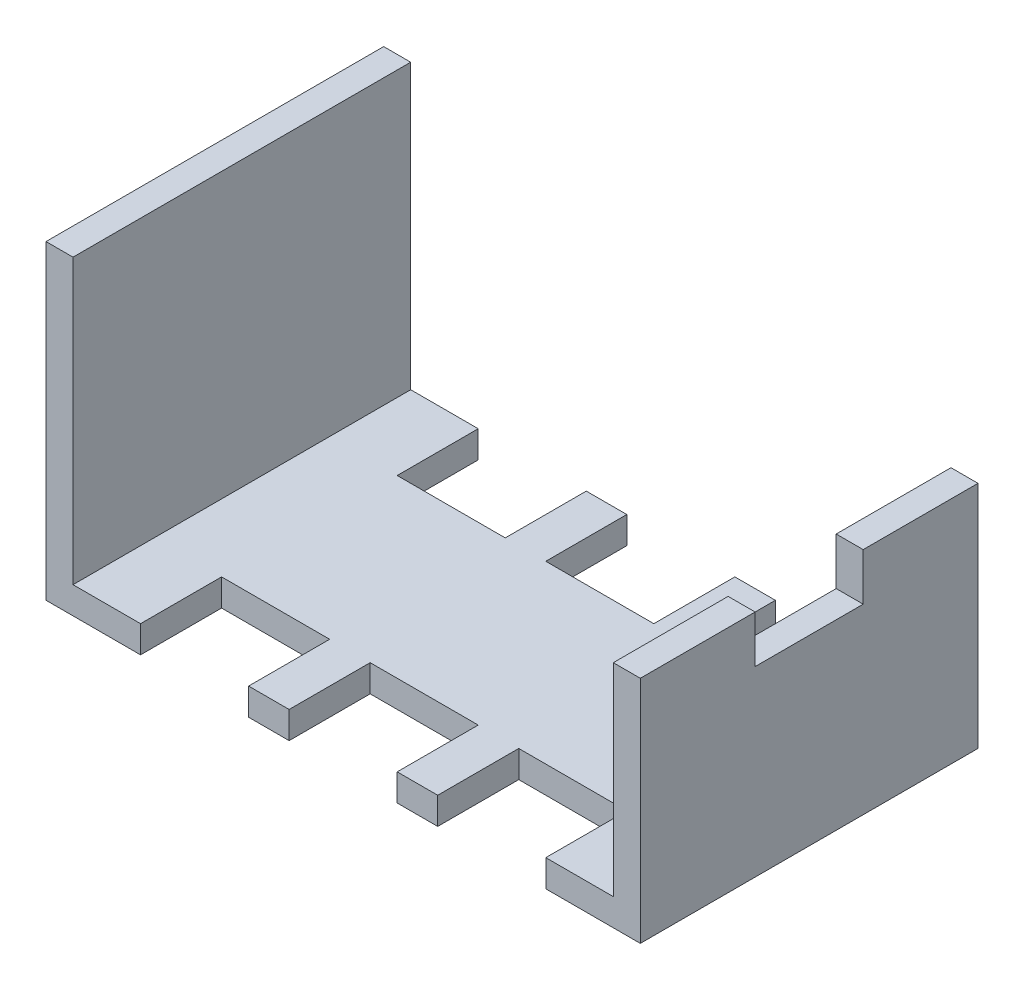
SolidWorks part; units mm, degrees
ref_plane "Front Plane" through (0, 0, 0) normal (0, 0, 1) x (1, 0, 0)
ref_plane "Top Plane" through (0, 0, 0) normal (0, 1, 0) x (1, 0, 0)
ref_plane "Right Plane" through (0, 0, 0) normal (1, 0, 0) x (0, 0, -1)
sketch "Sketch2" plane through (0, 0, 0) normal (0, 1, 0) x (1, 0, 0)
  line L1 (-22, 14.5) -> (22, 14.5)
  line L2 (-22, 14.5) -> (-22, -14.5)
  line L3 (-22, -14.5) -> (22, -14.5)
  line L4 (22, 14.5) -> (22, -14.5)
  line L5 (-22, 14.5) -> (22, -14.5) construction
  line L6 (-22, -14.5) -> (22, 14.5) construction
  point P0 (0, 0)
extrude "Boss-Extrude1" add sketch "Sketch2" along normal blind 23
sketch "Sketch3" plane through (0, 23, 0) normal (0, 1, 0) x (1, 0, 0)
  line L5 (-20, 12.5) -> (20, 12.5)
  line L6 (-20, 12.5) -> (-20, -12.5)
  line L7 (-20, -12.5) -> (20, -12.5)
  line L8 (20, 12.5) -> (20, -12.5)
  line L9 (-20, 12.5) -> (20, -12.5) construction
  line L10 (-20, -12.5) -> (20, 12.5) construction
  point P0 (0, 0)
  point P1 (0, 0)
extrude "Cut-Extrude1" cut sketch "Sketch3" against normal blind 21 contours L6 L5 L8 L7
sketch "Sketch4" plane through (0, 0, 14.5) normal (0, 0, 1) x (1, 0, 0)
  line L0 (-22, 23) -> (-20.1, 23) construction
  line L1 (-22, 23) -> (22, 23) construction
  line L2 (-20.1, 23) -> (-10.1, 23) construction
  line L3 (-10.1, 23) -> (-10.1, 17.2) construction
  line L4 (-10.1, 17.2) -> (10.6, 17.2) construction
  line L5 (-10.1, 17.2) -> (10.6, 17.2)
  line L6 (-10.1, 17.2) -> (-10.1, 19.2)
  line L7 (10.6, 17.2) -> (10.6, 19.2)
  line L8 (-10.1, 19.2) -> (10.6, 19.2)
  line L10 (-20.1, 23) -> (-20.1, 2) construction
  line L11 (-20.1, 2) -> (-15.1, 2) construction
  line L12 (20.2, 2) -> (20.2, 23) construction
  line L13 (-15.1, 2) -> (-15.1, 14.3) construction
  line L14 (-15.1, 14.3) -> (14.9, 14.3) construction
  line L16 (-15.1, 2) -> (14.9, 2)
  line L17 (-15.1, 2) -> (-15.1, 14.3)
  line L18 (-15.1, 14.3) -> (14.9, 14.3)
  line L19 (14.9, 2) -> (14.9, 14.3)
extrude "Cut-Extrude2" cut sketch "Sketch4" against normal blind 33 contours L5 L6 L8 L7
sketch "Sketch5" plane through (0, 0, 14.5) normal (0, 0, 1) x (1, 0, 0)
  line L0 (-22, 23) -> (-20, 23) construction
  line L1 (-22, 23) -> (22, 23) construction
  line L2 (-20, 23) -> (-20, 2) construction
  line L3 (-20, 2) -> (-15, 2) construction
  line L4 (-15, 2) -> (-15, 14.3) construction
  line L5 (-15, 14.3) -> (15, 14.3) construction
  line L7 (-15, 2) -> (15, 2)
  line L8 (-15, 2) -> (-15, 14.3)
  line L9 (-15, 14.3) -> (15, 14.3)
  line L10 (15, 2) -> (15, 14.3)
extrude "Cut-Extrude3" cut sketch "Sketch5" against normal blind 2
sketch "Sketch8" plane through (22, 0, 0) normal (1, 0, 0) x (0, 0, -1)
  line L0 (-14.5, 23) -> (-12.5, 23) construction
  line L1 (-14.5, 23) -> (14.5, 23) construction
  line L2 (-12.5, 17) -> (-4, 17)
  line L3 (-12.5, 23) -> (-12.5, 17) construction
  line L4 (-12.5, 17) -> (12.5, 17) construction
  line L5 (0, 17) -> (0, 15.25) construction
  line L6 (-12.5, 23) -> (12.5, 23)
  line L7 (-12.5, 23) -> (-12.5, 17)
  line L9 (12.5, 23) -> (12.5, 17)
  line L10 (4, 17) -> (12.5, 17)
  line L11 (-4, 13.5) -> (4, 13.5)
  line L12 (-4, 13.5) -> (-4, 17)
  line L14 (4, 13.5) -> (4, 17)
  line L15 (-4, 13.5) -> (4, 17) construction
  line L16 (-4, 17) -> (4, 13.5) construction
extrude "Cut-Extrude5" cut sketch "Sketch8" against normal blind 2
sketch "Sketch11" plane through (0, 0, -14.5) normal (0, 0, -1) x (-1, 0, 0)
  line L0 (-22, 0) -> (-22, 2) construction
  line L1 (-22, 23) -> (-22, 0) construction
  line L2 (-22, 2) -> (-16.1, 2) construction
  line L3 (-22, 2) -> (-20, 2) construction
  line L4 (-20, 2) -> (-16.1, 2)
  line L5 (-20, 2) -> (-20, 10.6)
  line L6 (-16.1, 2) -> (-16.1, 10.6)
  line L7 (-20, 10.6) -> (-16.1, 10.6)
  line L8 (-16.1, 2) -> (8.9, 2) construction
  line L10 (8.9, 2) -> (15.9, 2)
  line L11 (8.9, 2) -> (8.9, 3.5)
  line L12 (8.9, 3.5) -> (15.9, 3.5)
  line L13 (15.9, 2) -> (15.9, 3.5)
extrude "Cut-Extrude6" cut sketch "Sketch11" against normal blind 2
sketch "Sketch13" plane through (0, 2, 0) normal (0, 1, 0) x (1, 0, 0)
  line L0 (-15, -12.5) -> (15, -12.5) construction
  line L6 (-20, -12.5) -> (-15, -12.5) construction
  line L7 (-20, -12.5) -> (-15, -12.5) construction
  line L8 (0, 0) -> (5, 0) construction
  line L13 (-7, -12.5) -> (-4, -12.5) construction
  line L14 (-15, -12.5) -> (-7, -12.5)
  line L15 (-15, -12.5) -> (-15, -6.5)
  line L16 (-15, -6.5) -> (-7, -6.5)
  line L17 (-7, -12.5) -> (-7, -6.5)
  line L18 (4, -12.5) -> (7, -12.5) construction
  line L19 (-4, -12.5) -> (4, -12.5)
  line L20 (-4, -12.5) -> (-4, -6.5)
  line L21 (-4, -6.5) -> (4, -6.5)
  line L22 (4, -12.5) -> (4, -6.5)
  line L23 (7, 6.5) -> (15, 6.5)
  line L24 (7, -12.5) -> (15, -12.5)
  line L25 (7, -12.5) -> (7, -6.5)
  line L26 (7, -6.5) -> (15, -6.5)
  line L27 (15, -12.5) -> (15, -6.5)
  line L28 (15, 12.5) -> (15, 6.5)
  line L29 (7, 12.5) -> (15, 12.5)
  line L30 (7, 12.5) -> (7, 6.5)
  line L31 (-15, 6.5) -> (-7, 6.5)
  line L32 (-7, 12.5) -> (-7, 6.5)
  line L33 (-15, 12.5) -> (-7, 12.5)
  line L34 (-15, 12.5) -> (-15, 6.5)
  line L35 (-4, 6.5) -> (4, 6.5)
  line L36 (4, 12.5) -> (4, 6.5)
  line L37 (-4, 12.5) -> (4, 12.5)
  line L38 (-4, 12.5) -> (-4, 6.5)
extrude "Cut-Extrude8" cut sketch "Sketch13" against normal blind 2 contours L16 L17 L14 L15 | L22 L21 L20 L19 | L25 L24 L27 L26 | L23 L28 L29 L30 | L35 L36 L37 L38 | L31 L32 L33 L34
sketch "Sketch14" plane through (0, 23, 0) normal (0, 1, 0) x (1, 0, 0)
  line L1 (-22, -14.5) -> (22, -14.5)
  line L2 (-22, -14.5) -> (-22, -12.5)
  line L3 (-22, -12.5) -> (22, -12.5)
  line L4 (22, -14.5) -> (22, -12.5)
  line L5 (-22, 14.5) -> (22, 14.5)
  line L6 (-22, 14.5) -> (-22, 12.5)
  line L7 (-22, 12.5) -> (22, 12.5)
  line L8 (22, 14.5) -> (22, 12.5)
extrude "Cut-Extrude9" cut sketch "Sketch14" against normal blind 23
